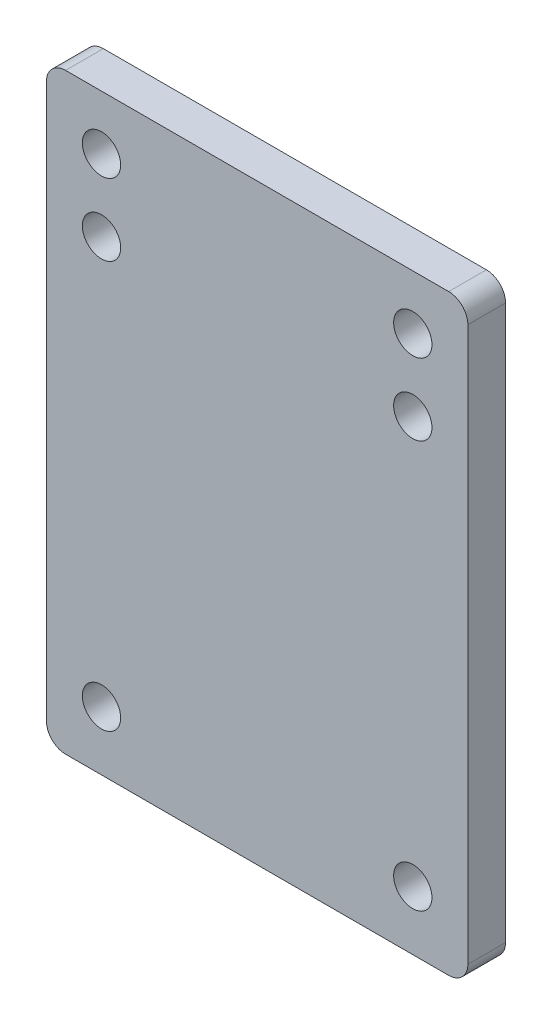
SolidWorks part; units mm, degrees
material "BUTYL"
ref_plane "Normal Z (Oben)" through (0, 0, 0) normal (0, 0, 1) x (1, 0, 0)
ref_plane "Normal Y" through (0, 0, 0) normal (0, 1, 0) x (1, 0, 0)
ref_plane "Normal X" through (0, 0, 0) normal (1, 0, 0) x (0, 0, -1)
sketch "Skizze1" plane through (0, 0, 0) normal (0, 0, 1) x (1, 0, 0)
  line L0 (9.8201, -30.2764) -> (9.8201, -39.1655) construction
  line L1 (9.8668, -39.1664) -> (26.3737, -39.1664)
  line L2 (28.9137, -36.6229) -> (28.9137, 36.8211)
  line L3 (26.3737, 39.3611) -> (-24.4263, 39.3611)
  line L4 (-26.9663, 36.8211) -> (-26.9663, -36.6229)
  line L5 (-24.4263, -39.1664) -> (-7.9194, -39.1664)
  line L6 (-7.8727, -39.1655) -> (-7.8727, -30.2764) construction
  line L7 (-5.3312, -27.7364) -> (7.2786, -27.7364) construction
  line L8 (-7.8727, -39.1655) -> (9.8668, -39.1664)
  arc A0 (28.9137, 36.8211) -> (26.3737, 39.3611) centre (26.3737, 36.8211) ccw
  arc A1 (-24.4263, 39.3611) -> (-26.9663, 36.8211) centre (-24.4263, 36.8211) ccw
  circle A2 centre (-19.6638, -31.3432) radius 2.54
  circle A3 centre (21.6112, -31.3432) radius 2.54
  circle A4 centre (21.6112, 32.1568) radius 2.54
  circle A5 centre (21.6112, 22.6318) radius 2.54
  circle A6 centre (-19.6638, 22.6318) radius 2.54
  circle A7 centre (-19.6638, 32.1568) radius 2.54
  ellipse E0 centre (9.8645, -37.8946) end of major axis (10.5701, -38.9536) minor radius 1.27 (9.8201, -39.1655) -> (9.8668, -39.1664) ccw
  ellipse E1 centre (26.3737, -36.6229) end of major axis (26.3737, -34.0794) minor radius 2.54 (26.3737, -39.1664) -> (28.9137, -36.6229) ccw
  ellipse E2 centre (-24.4263, -36.6229) end of major axis (-24.4263, -34.0794) minor radius 2.54 (-26.9663, -36.6229) -> (-24.4263, -39.1664) ccw
  ellipse E3 centre (-7.9171, -37.8946) end of major axis (-8.6227, -38.9536) minor radius 1.27 (-7.9194, -39.1664) -> (-7.8727, -39.1655) ccw
  ellipse E4 centre (-5.3312, -30.2764) end of major axis (-2.7896, -30.2764) minor radius 2.54 (-5.3312, -27.7364) -> (-7.8727, -30.2764) ccw construction
  ellipse E5 centre (7.2786, -30.2764) end of major axis (9.8201, -30.2764) minor radius 2.54 (9.8201, -30.2764) -> (7.2786, -27.7364) ccw construction
extrude "Aufsatz-Linear austragen1" add sketch "Skizze1" along normal blind 5
